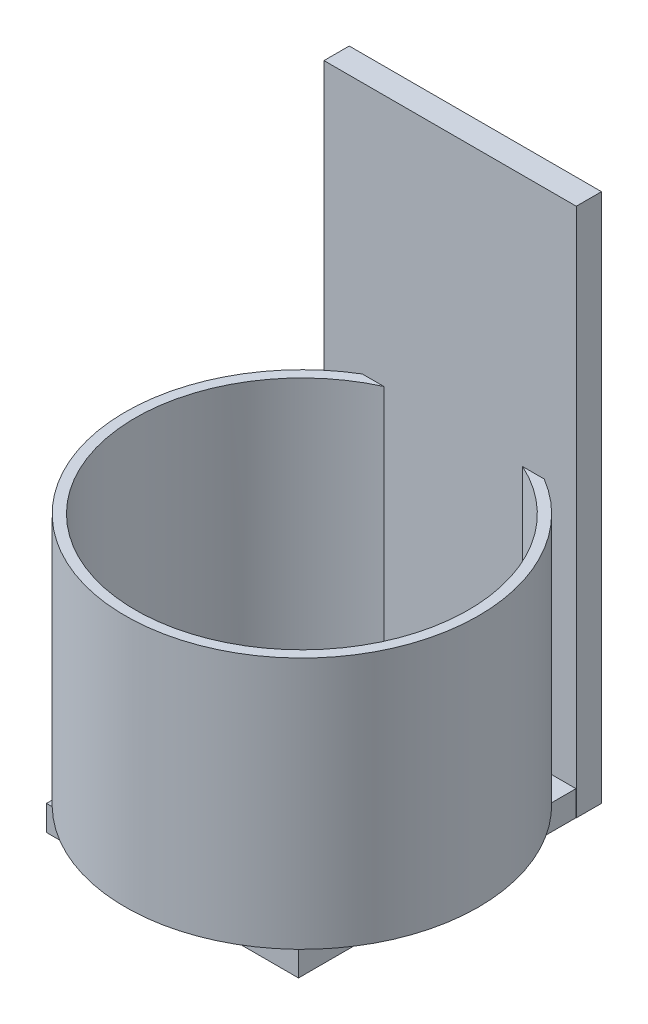
SolidWorks part; units mm, degrees
material "ABS"
ref_plane "Front Plane" through (0, 0, 0) normal (0, 0, 1) x (1, 0, 0)
ref_plane "Top Plane" through (0, 0, 0) normal (0, 1, 0) x (1, 0, 0)
ref_plane "Right Plane" through (0, 0, 0) normal (1, 0, 0) x (0, 0, -1)
sketch "Sketch1" plane through (0, 0, 0) normal (0, 0, 1) x (1, 0, 0)
  line L1 (0, 0) -> (63.5, 0)
  line L2 (0, 0) -> (0, -127)
  line L3 (0, -127) -> (63.5, -127)
  line L4 (63.5, 0) -> (63.5, -127)
  dimension "D1" = 127
  dimension "D2" = 63.5
extrude "Boss-Extrude1" add sketch "Sketch1" along normal blind 6.35
sketch "Sketch2" plane through (0, -127, 0) normal (0, -1, 0) x (1, 0, 0)
  line L2 (0, 0) -> (63.4303, 0)
  line L3 (0, 0) -> (0, 76.2)
  line L4 (0, 76.2) -> (63.4303, 76.2)
  line L5 (63.4303, 0) -> (63.4303, 76.2)
  dimension "D1" = 76.2
extrude "Boss-Extrude2" add sketch "Sketch2" along normal blind 6.35 separate body
sketch "Sketch3" plane through (0, -127, 0) normal (0, -1, 0) x (1, 0, 0)
  line L4 (0, 0) -> (63.5, 0)
  line L5 (63.5, 0) -> (63.5, 6.35)
  line L6 (63.5, 6.35) -> (0, 6.35)
  line L7 (0, 6.35) -> (0, 0)
  line L8 (0, 0) -> (63.5, 0)
  line L9 (63.5, 0) -> (63.5, 6.35)
  line L10 (63.5, 6.35) -> (0, 6.35)
  line L11 (0, 6.35) -> (0, 0)
  dimension "D1" = 0
extrude "Boss-Extrude3" add sketch "Sketch3" along normal blind 6.35
ref_plane "Plane1" through (0, -63.5, 0) normal (0, 1, 0) x (1, 0, 0)
sketch "Sketch4" plane through (0, -63.5, 0) normal (0, 1, 0) x (1, 0, 0)
  line L0 (0, 0) -> (63.5, 0) construction
  circle A0 centre (32.5377, -44.45) radius 44.45
  circle A1 centre (32.5377, -44.45) radius 41.91
  point P0 (32.5377, -50.1897)
  point P14 (0, 0)
  dimension "D1" = 88.9
  dimension "D2" = 2.54
extrude "Boss-Extrude4" add sketch "Sketch4" against normal up to surface (63.5 mm away) up to face at (31.7152, -127, 41.275)
